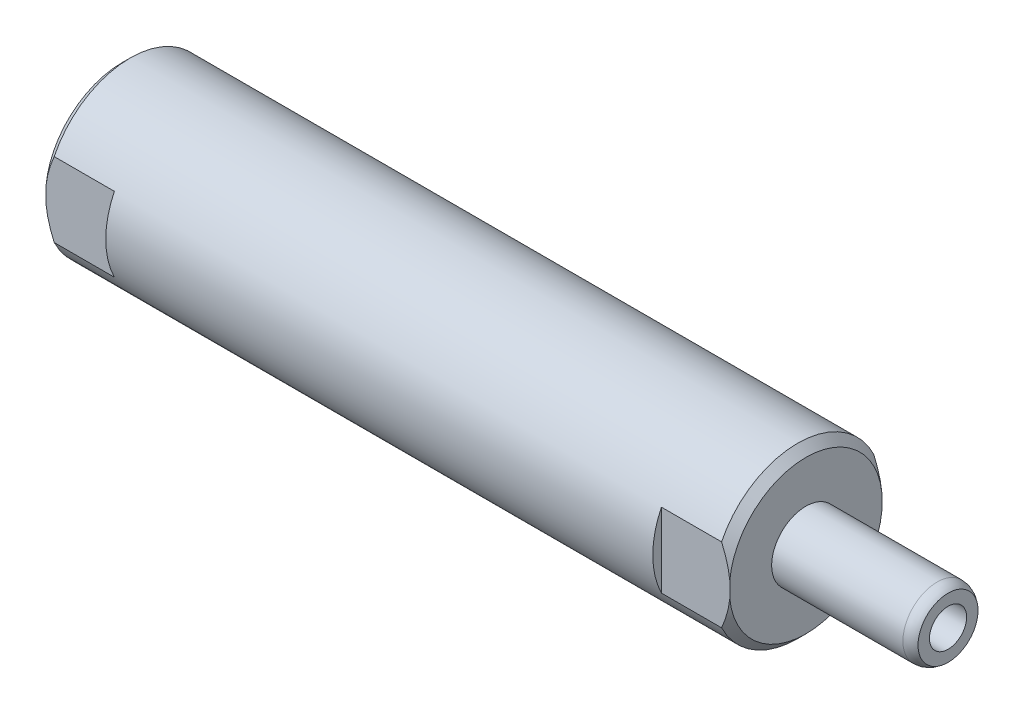
SolidWorks part; units mm, degrees
material "Alloy Steel"
ref_plane "Front Plane" through (0, 0, 0) normal (0, 0, 1) x (1, 0, 0)
ref_plane "Top Plane" through (0, 0, 0) normal (0, 1, 0) x (1, 0, 0)
ref_plane "Right Plane" through (0, 0, 0) normal (1, 0, 0) x (0, 0, -1)
ref_plane "Plane1" through (0, 0, 0) normal (0, 0, -1) x (-1, 0, 0)
sketch "Sketch1" plane through (0, 0, 0) normal (0, 0, -1) x (-1, 0, 0)
  line L0 (-76.708, 2.7869) -> (-76.708, 0)
  line L1 (-76.708, 0) -> (0, 0)
  line L2 (0, 0) -> (0, 7.8613)
  line L4 (0, 7.8613) -> (-63.5, 7.8613)
  line L6 (-63.5, 7.8613) -> (-63.5, 3.175)
  line L7 (-63.5, 3.175) -> (-75.692, 3.175)
  line L8 (-76.708, 0) -> (0, 0) construction
  line L9 (0, 0) -> (6.3339, 0) construction
  arc A0 (-75.692, 3.175) -> (-76.708, 2.7869) centre (-75.692, 1.651) ccw
  dimension "D6" = 1.524
  dimension "D1" = 15.7226
  dimension "D4" = 6.35
  dimension "D5" = 1.016
  dimension "D7" = 13.208
  dimension "D8" = 63.5
revolve "Revolve1" add sketch "Sketch1" angle 360 about L8
sketch "Sketch2" plane through (0, 0, 0) normal (0, 0, -1) x (-1, 0, 0)
  line L0 (-13.97, 4.9784) -> (-13.97, 0)
  line L1 (-13.97, 0) -> (0, 0)
  line L2 (0, 0) -> (0, 6.1849)
  line L3 (0, 6.1849) -> (-2.5527, 5.6423)
  line L4 (-2.5527, 5.6423) -> (-3.2166, 4.9784)
  line L5 (-3.2166, 4.9784) -> (-13.97, 4.9784)
  line L6 (-13.97, 0) -> (0, 0) construction
revolve "Cut-Revolve1" cut sketch "Sketch2" angle 360 about L6
sketch "Sketch3" plane through (0, 0, 0) normal (0, 0, -1) x (-1, 0, 0)
  line L0 (-76.708, 1.7272) -> (-76.708, 0)
  line L1 (-76.708, 0) -> (-70.358, 0)
  line L2 (-70.358, 0) -> (-71.3958, 1.7272)
  line L3 (-71.3958, 1.7272) -> (-76.708, 1.7272)
  line L4 (-66.3139, 0) -> (-46.9899, 0) construction
  line L5 (-76.708, 2.7869) -> (-76.708, -2.7869) construction
  dimension "D1" = 3.4544
  dimension "D2" = 6.35
  dimension "D3" = 59
revolve "Cut-Revolve2" cut sketch "Sketch3" angle 360 about L4
chamfer "Chamfer1" distance 0.762 angle 45 2 edges at (0, 0, 7.8613) (63.5, 0, 7.8613)
sketch "Sketch5" plane through (0, 0, 0) normal (0, 1, 0) x (1, 0, 0)
  line L0 (0, 0) -> (18.2862, 0) construction
  line L1 (0, 7.0612) -> (6.35, 7.0612)
  line L2 (6.35, 7.0612) -> (6.35, 7.8613)
  line L3 (62.738, 7.8613) -> (0.762, 7.8613) construction
  line L4 (6.35, 7.8613) -> (0, 7.8613)
  line L5 (0, 7.8613) -> (0, 7.0612)
  line L6 (0, 7.0993) -> (0, -7.0993) construction
  line L7 (0, -7.8613) -> (0, -7.0612)
  line L8 (6.35, -7.8613) -> (0, -7.8613)
  line L9 (6.35, -7.0612) -> (6.35, -7.8613)
  line L10 (0, -7.0612) -> (6.35, -7.0612)
  dimension "D1" = 90
  dimension "D2" = 6.35
  dimension "D3" = 14.1224
extrude "Cut-Extrude1" cut sketch "Sketch5" against normal through all and the other way through all
sketch "Sketch6" plane through (0, 0, 0) normal (0, 1, 0) x (1, 0, 0)
  line L0 (63.5, -7.0993) -> (63.5, 7.0993) construction
  line L1 (63.5, 7.0612) -> (57.15, 7.0612)
  line L2 (63.5, 7.0612) -> (63.5, 7.8613)
  line L3 (63.5, 7.8613) -> (57.15, 7.8613)
  line L4 (57.15, 7.0612) -> (57.15, 7.8613)
  line L5 (62.738, 7.8613) -> (6.35, 7.8613) construction
  line L6 (6.35, -7.8613) -> (62.738, -7.8613) construction
  line L7 (63.5, -7.0612) -> (57.15, -7.0612)
  line L8 (63.5, -7.0612) -> (63.5, -7.8613)
  line L9 (63.5, -7.8613) -> (57.15, -7.8613)
  line L10 (57.15, -7.0612) -> (57.15, -7.8613)
  dimension "D1" = 6.35
  dimension "D2" = 14.1224
extrude "Cut-Extrude2" cut sketch "Sketch6" against normal through all and the other way through all
